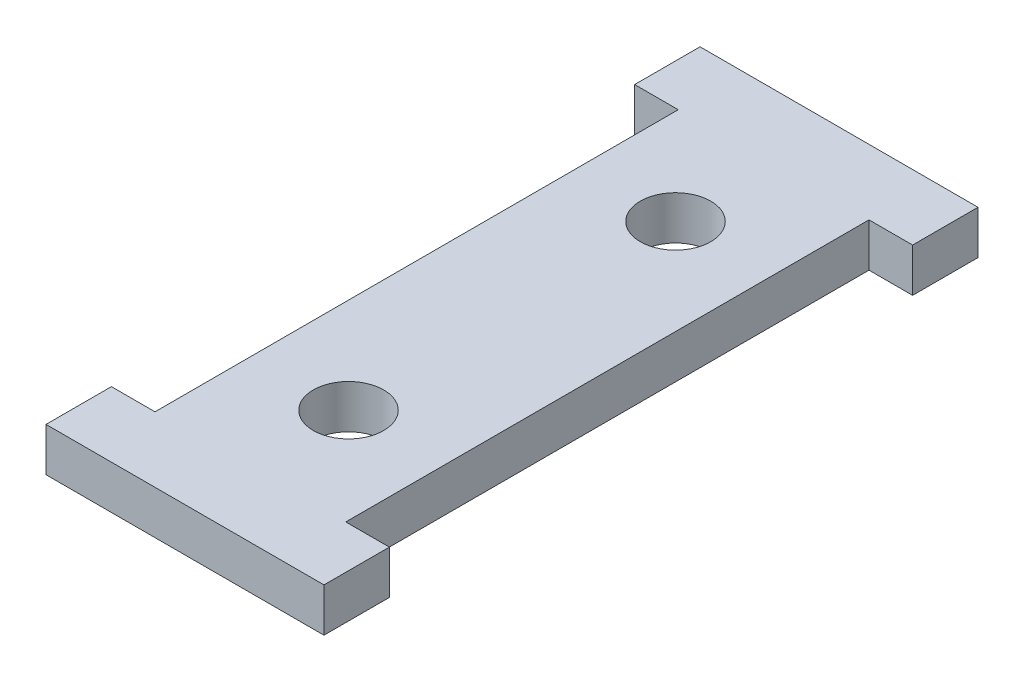
SolidWorks part; units mm, degrees
material "Pine"
ref_plane "Front Plane" through (0, 0, 0) normal (0, 0, 1) x (1, 0, 0)
ref_plane "Top Plane" through (0, 0, 0) normal (0, 1, 0) x (1, 0, 0)
ref_plane "Right Plane" through (0, 0, 0) normal (1, 0, 0) x (0, 0, -1)
sketch "Sketch1" plane through (0, 0, 0) normal (0, 1, 0) x (1, 0, 0)
  line L4 (-16.1925, 0) -> (16.1925, 0)
  line L5 (-16.1925, 0) -> (-16.1925, 7.62)
  line L6 (-16.1925, 7.62) -> (-11.1125, 7.62)
  line L7 (-11.1125, 7.62) -> (-11.1125, 68.58)
  line L8 (-11.1125, 68.58) -> (-16.1925, 68.58)
  line L9 (-16.1925, 68.58) -> (-16.1925, 76.2)
  line L10 (-16.1925, 76.2) -> (16.1925, 76.2)
  line L11 (16.1925, 76.2) -> (16.1925, 68.58)
  line L12 (16.1925, 68.58) -> (11.1125, 68.58)
  line L13 (11.1125, 68.58) -> (11.1125, 7.62)
  line L14 (11.1125, 7.62) -> (16.1925, 7.62)
  line L15 (16.1925, 7.62) -> (16.1925, 0)
  point P4 (0, 0)
  dimension "D1" = 7.62
  dimension "D2" = 76.2
  dimension "D3" = 22.225
  dimension "D4" = 5.08
extrude "Boss-Extrude1" add sketch "Sketch1" along normal blind 5.08
hole_wizard "P (0.323) Diameter Hole1" positions "Sketch2" profile "Sketch3" hole size "P" standard "ANSI Inch"
sketch "Sketch2" plane through (0, 5.08, 0) normal (0, 1, 0) x (1, 0, 0)
  line L2 (-11.1125, 38.1) -> (11.1125, 38.1) construction
  line L3 (-11.1125, 68.58) -> (-11.1125, 7.62) construction
  line L4 (11.1125, 7.62) -> (11.1125, 68.58) construction
  point P0 (0, 57.15)
  point P19 (0, 19.05)
  dimension "D1" = 38.1
sketch "Sketch3" plane through (0, 5.08, -57.15) normal (1, 0, 0) x (0, 0, 1)
  line L0 (0, 0) -> (0, 18.9748)
  line L1 (0, 18.9748) -> (4.1021, 16.51)
  line L2 (4.1021, 16.51) -> (4.1021, 0)
  line L5 (4.1021, 0) -> (0, 0)
  line L10 (0, 18.9748) -> (-4.1021, 16.51) construction
  line L11 (0, -6.35) -> (0, 107.95) construction
  dimension "Hole Dia." = 8.2042
  dimension "Hole Depth" = 16.51
  dimension "Drill Angle" = 118
